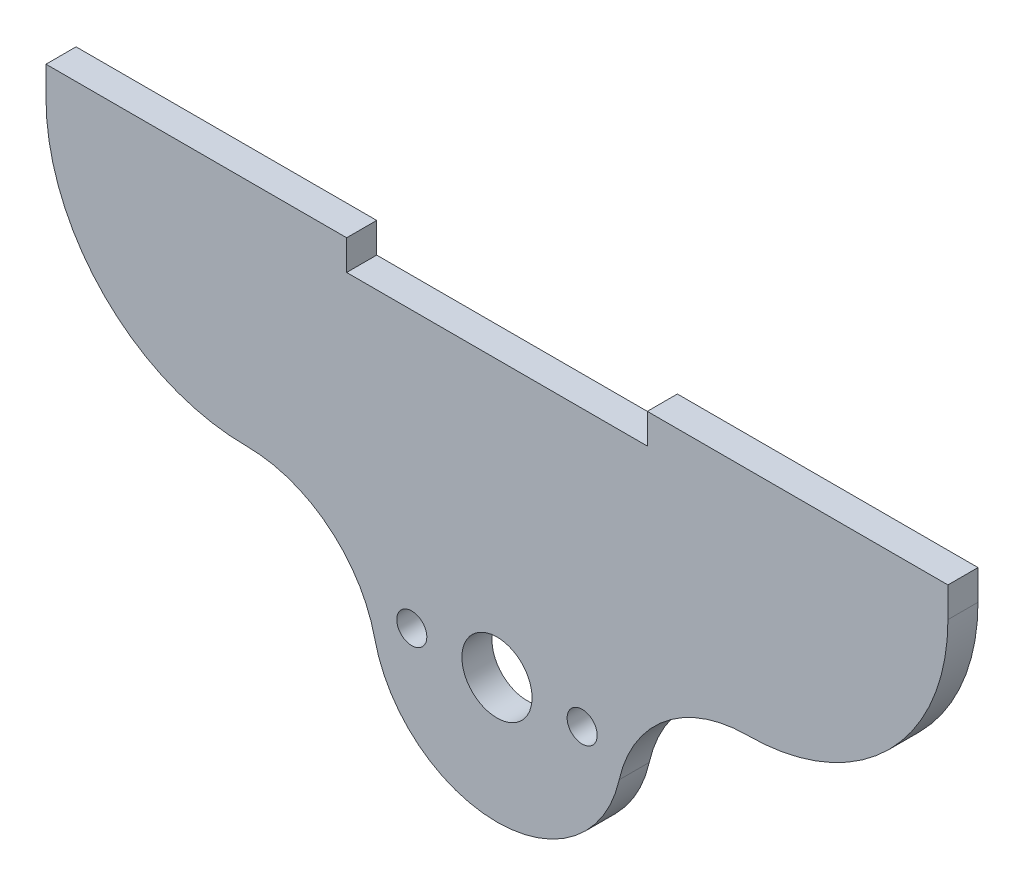
SolidWorks part; units mm, degrees
ref_plane "Front Plane" through (0, 0, 0) normal (0, 0, 1) x (1, 0, 0)
ref_plane "Top Plane" through (0, 0, 0) normal (0, 1, 0) x (1, 0, 0)
ref_plane "Right Plane" through (0, 0, 0) normal (1, 0, 0) x (0, 0, -1)
sketch "Sketch1" plane through (0, 0, 0) normal (0, 0, 1) x (1, 0, 0)
  line L0 (-8.5, 0) -> (8.5, 0) construction
  line L1 (-15, 27.5) -> (15, 27.5)
  line L2 (-45, 27.5) -> (-45, 28.6955) construction
  line L3 (45, 27.5) -> (45, 30.5) construction
  line L4 (-25, 7.5) -> (-49.9345, 7.5) construction
  line L5 (25, 7.5) -> (47.5049, 7.5) construction
  line L8 (-45, 27.5) -> (-45, 30.5)
  line L9 (-45, 30.5) -> (-15, 30.5)
  line L10 (-15, 27.5) -> (-15, 30.5)
  line L12 (45, 27.5) -> (45, 30.5)
  line L13 (45, 30.5) -> (15, 30.5)
  line L14 (15, 27.5) -> (15, 30.5)
  circle A0 centre (-8.5, 0) radius 1.5
  circle A1 centre (8.5, 0) radius 1.5
  circle A2 centre (0, 0) radius 3.5
  circle A3 centre (0, 0) radius 12.5 construction
  arc A4 (-12.1951, -2.7439) -> (12.1951, -2.7439) centre (0, 0) ccw
  arc A5 (-45, 27.5) -> (-25, 7.5) centre (-25, 27.5) ccw
  arc A6 (-12.1951, -2.7439) -> (-25, 7.5) centre (-25, -5.625) ccw
  arc A7 (12.1951, -2.7439) -> (25, 7.5) centre (25, -5.625) cw
  arc A8 (25, 7.5) -> (45, 27.5) centre (25, 27.5) ccw
  point P4 (0, 0)
  point P10 (0, 27.5)
  point P12 (0, 12.5)
  dimension "D1" = 3
  dimension "D3" = 7
  dimension "D5" = 25
  dimension "D2" = 17
  dimension "D4" = 90
  dimension "D6" = 15
  dimension "D7" = 20
  dimension "D8" = 3
extrude "Boss-Extrude1" add sketch "Sketch1" along normal blind 3
